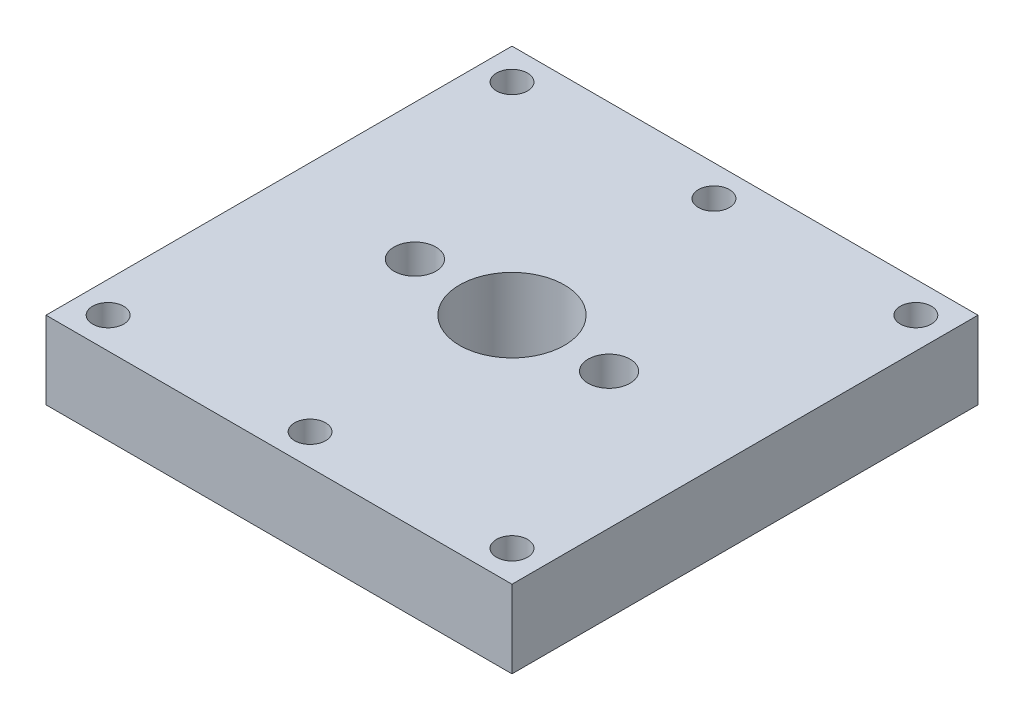
SolidWorks part; units mm, degrees
ref_plane "Front Plane" through (0, 0, 0) normal (0, 0, 1) x (1, 0, 0)
ref_plane "Top Plane" through (0, 0, 0) normal (0, 1, 0) x (1, 0, 0)
ref_plane "Right Plane" through (0, 0, 0) normal (1, 0, 0) x (0, 0, -1)
sketch "Sketch2" plane through (0, 0, 0) normal (0, 1, 0) x (1, 0, 0)
  line L1 (30, -30) -> (-30, -30)
  line L2 (30, -30) -> (30, 30)
  line L3 (30, 30) -> (-30, 30)
  line L4 (-30, -30) -> (-30, 30)
  line L5 (30, -30) -> (-30, 30) construction
  line L6 (30, 30) -> (-30, -30) construction
  point P0 (0, 0)
  dimension "D1" = 60
  dimension "D2" = 60
extrude "Boss-Extrude1" add sketch "Sketch2" along normal blind 10
sketch "Sketch3" plane through (0, 10, 0) normal (0, 1, 0) x (1, 0, 0)
  line L0 (30, 30) -> (-30, 30) construction
  line L1 (-30, 30) -> (-30, -30) construction
  line L2 (30, -30) -> (30, 30) construction
  line L4 (-30, -30) -> (30, -30) construction
  circle A0 centre (-26, 26) radius 2
  circle A1 centre (-26, -26) radius 2
  circle A2 centre (0, -26) radius 2
  circle A3 centre (26, -26) radius 2
  circle A4 centre (26, 26) radius 2
  circle A5 centre (0, 26) radius 2
  point P18 (0, -30)
  dimension "D1" = 4
  dimension "D2" = 4
  dimension "D3" = 4
  dimension "D4" = 4
  dimension "D5" = 4
  dimension "D6" = 4
  dimension "D7" = 4
  dimension "D8" = 4
  dimension "D9" = 4
  dimension "D10" = 4
  dimension "D11" = 4
  dimension "D12" = 4
  dimension "D13" = 4
  dimension "D14" = 4
  dimension "D15" = 4
  dimension "D16" = 4
extrude "Cut-Extrude1" cut sketch "Sketch3" against normal blind 10
sketch "Sketch5" plane through (0, 10, 0) normal (0, 1, 0) x (1, 0, 0)
  circle A0 centre (12.5, 0) radius 2.7
  circle A1 centre (-12.5, 0) radius 2.7
  dimension "D1" = 5.4
  dimension "D2" = 5.4
  dimension "D3" = 25
  dimension "D4" = 12.5
extrude "Cut-Extrude3" cut sketch "Sketch5" against normal blind 7
sketch "Sketch6" plane through (0, 0, 0) normal (0, -1, 0) x (1, 0, 0)
  circle A0 centre (12.5, 0) radius 0.5
  circle A1 centre (-12.5, 0) radius 0.5
  dimension "D1" = 1
  dimension "D2" = 1
extrude "Cut-Extrude4" cut sketch "Sketch6" against normal blind 3
sketch "Sketch7" plane through (0, 10, 0) normal (0, 1, 0) x (1, 0, 0)
  circle A0 centre (0, 0) radius 6.75
  dimension "D1" = 13.5
extrude "Cut-Extrude5" cut sketch "Sketch7" against normal blind 10
